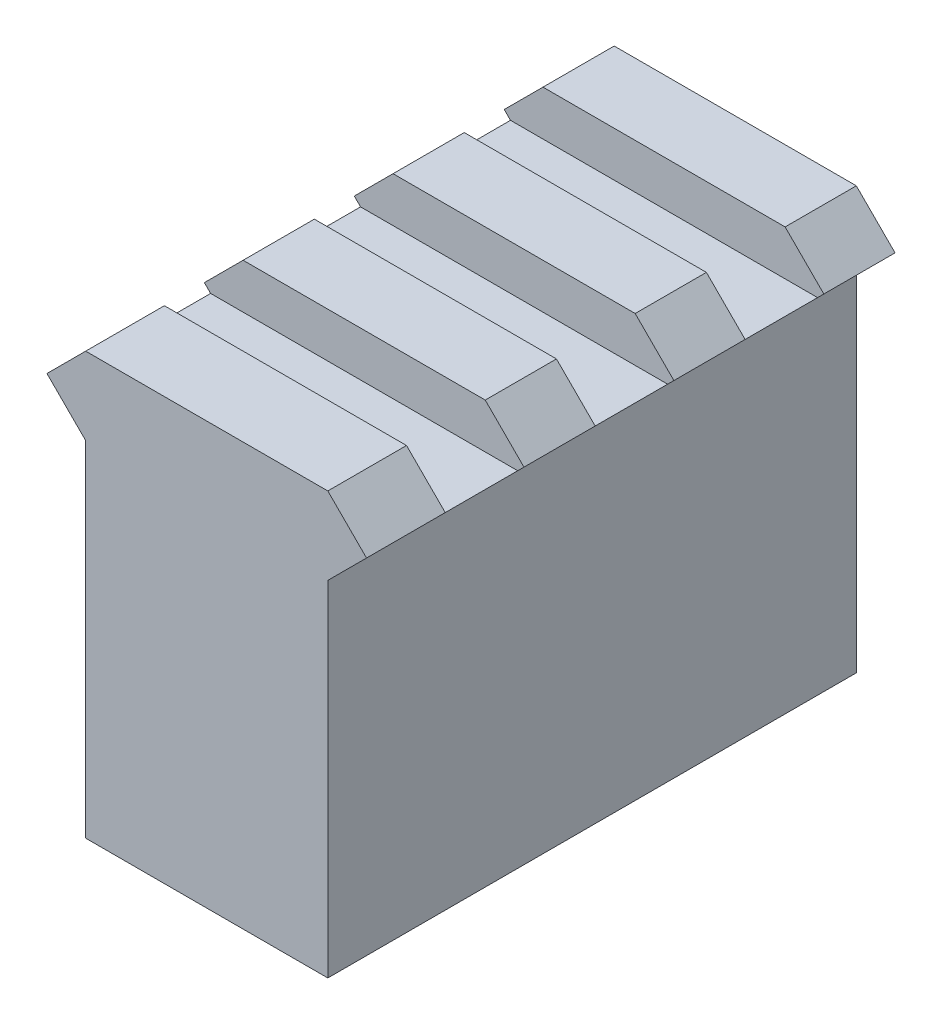
SolidWorks part; units mm, degrees
material "6061 Alloy"
ref_plane "Front Plane" through (0, 0, 0) normal (0, 0, 1) x (1, 0, 0)
ref_plane "Top Plane" through (0, 0, 0) normal (0, 1, 0) x (1, 0, 0)
ref_plane "Right Plane" through (0, 0, 0) normal (1, 0, 0) x (0, 0, -1)
sketch "Sketch1" plane through (0, 0, 0) normal (0, 0, 1) x (1, 0, 0)
  line L0 (-8.0748, 0) -> (8.0748, 0)
  line L1 (8.0748, 0) -> (8.0748, 22.9672)
  line L2 (8.0748, 22.9672) -> (10.6576, 25.55)
  line L3 (10.6576, 25.55) -> (8.0748, 28.1328)
  line L4 (8.0748, 28.1328) -> (-8.0748, 28.1328)
  line L5 (-17.8672, 23.9672) -> (17.8672, 23.9672) construction
  line L6 (-0.5726, 34.75) -> (19.7788, 34.75) construction
  line L7 (0, 0) -> (0, 17.3353) construction
  line L11 (-10.6576, 25.55) -> (-8.0748, 28.1328)
  line L12 (-8.0748, 22.9672) -> (-10.6576, 25.55)
  line L13 (-8.0748, 0) -> (-8.0748, 22.9672)
  point P12 (0, 28.1328)
  dimension "D3" = 45
  dimension "D4" = 45
  dimension "D5" = 1
  dimension "D6" = 4.1656
  dimension "D7" = 9.2
  dimension "D8" = 34.75
extrude "Boss-Extrude1" add sketch "Sketch1" along normal blind 35.25 contours L4 L11 L12 L13 L0 L1 L2 L3
hole_wizard "1/4-20 Tapped Hole1" positions "Sketch2" profile "Sketch3" tap size "1/4-20" standard "ANSI Inch"
sketch "Sketch2" plane through (0, 0, 0) normal (0, -1, 0) x (-1, 0, 0)
  line L1 (0, -35.25) -> (0, 0) construction
  line L2 (8.0748, -35.25) -> (-8.0748, -35.25) construction
  point P0 (0, -8.25)
  point P2 (0, -28.25)
  dimension "D1" = 20
  dimension "D2" = 7
sketch "Sketch3" plane through (0, 0, 8.25) normal (1, 0, 0) x (0, 0, -1)
  line L0 (0, 0) -> (0, 16.5338)
  line L1 (0, 16.5338) -> (2.5527, 15)
  line L2 (2.5527, 15) -> (2.5527, 0)
  line L5 (2.5527, 0) -> (0, 0)
  line L10 (0, 16.5338) -> (-2.5527, 15) construction
  line L11 (0, -6.35) -> (0, 107.95) construction
  dimension "Tap Drill Dia." = 5.1054
  dimension "Tap Drill Depth" = 15
  dimension "Drill Angle" = 118
sketch "Sketch4" plane through (0, 28.1328, 0) normal (0, 1, 0) x (1, 0, 0)
  line L0 (8.0748, 0) -> (-8.0748, 0) construction
  line L1 (-14.315, -10) -> (14.315, -10)
  line L2 (-14.315, -10) -> (-14.315, -4.75)
  line L3 (-14.315, -4.75) -> (14.315, -4.75)
  line L4 (14.315, -10) -> (14.315, -4.75)
  line L5 (-14.315, -10) -> (14.315, -4.75) construction
  line L6 (-14.315, -4.75) -> (14.315, -10) construction
  line L7 (-14.315, -20) -> (14.315, -20)
  line L8 (-14.315, -20) -> (-14.315, -14.75)
  line L9 (-14.315, -14.75) -> (14.315, -14.75)
  line L10 (14.315, -20) -> (14.315, -14.75)
  line L11 (-14.315, -30) -> (14.315, -30)
  line L12 (-14.315, -30) -> (-14.315, -24.75)
  line L13 (-14.315, -24.75) -> (14.315, -24.75)
  line L14 (14.315, -30) -> (14.315, -24.75)
  point P0 (0, -7.375)
  line M4 (-8.0748, 0) -> (-8.0748, -35.25)
  line M6 (8.0748, -35.25) -> (8.0748, 0)
  dimension "D1" = 10
  dimension "D2" = 5.25
  dimension "D3" = 3
extrude "Cut-Extrude1" cut sketch "Sketch4" against normal blind 3 contours L9 L8 L7 M4 | L9 L7 M4 M6 | L7 L10 L9 M6 | L13 L12 L11 M4 | L13 L11 M4 M6 | L11 L14 L13 M6 | L3 L4 L1 L2
